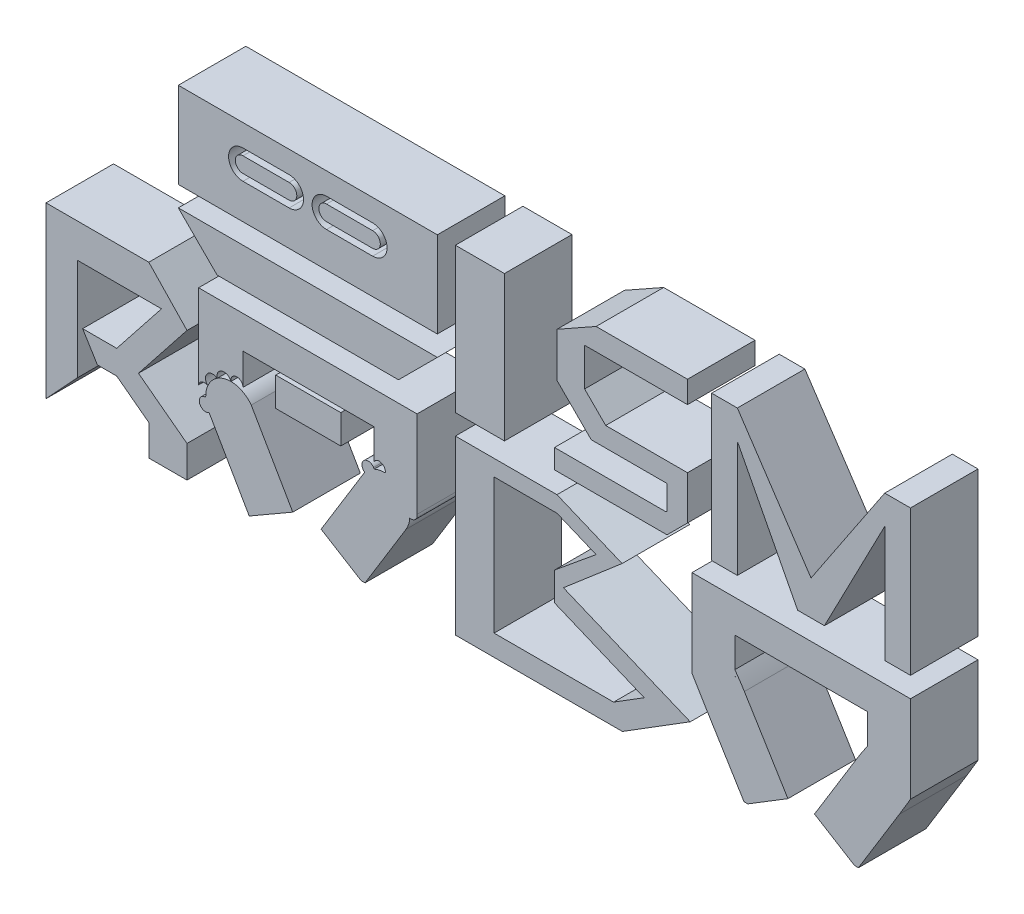
SolidWorks part; units mm, degrees
ref_plane "Front Plane" through (0, 0, 0) normal (0, 0, 1) x (1, 0, 0)
ref_plane "Top Plane" through (0, 0, 0) normal (0, 1, 0) x (1, 0, 0)
ref_plane "Right Plane" through (0, 0, 0) normal (1, 0, 0) x (0, 0, -1)
sketch "Sketch1" plane through (0, 0, 0) normal (0, 0, 1) x (1, 0, 0)
  line L0 (-96.2601, 0.8841) -> (-96.2601, 8.7422)
  line L1 (-108.1725, -11.9352) -> (-108.1725, 51.8543)
  line L2 (-108.1725, 51.8543) -> (-69.5108, 51.8543)
  line L3 (-69.5108, 51.8543) -> (-55.143, 36.8142)
  line L4 (-55.143, 36.8142) -> (-73.3959, 13.7377)
  line L5 (-73.3959, 13.7377) -> (-55.143, 0)
  line L6 (-55.143, 0) -> (-55.143, -11.9352)
  line L7 (-55.143, -11.9352) -> (-69.3611, -11.9352)
  line L8 (-69.3611, -11.9352) -> (-69.3611, -0.4586)
  line L9 (-69.3611, -0.4586) -> (-81.5859, 8.7422)
  line L10 (-81.5651, 17.7726) -> (-94.3869, 17.7726)
  line L11 (-94.3869, 17.7726) -> (-88.8416, 8.7422)
  line L12 (-88.8416, 8.7422) -> (-81.5859, 8.7422)
  line L13 (-81.5651, 17.7726) -> (-64.7268, 39.0605)
  line L14 (-64.7268, 39.0605) -> (-96.2601, 39.0605)
  line L15 (-96.2601, 39.0605) -> (-96.2601, 8.7422)
  line L16 (-96.2601, 0.8841) -> (-108.1725, -11.9352)
  line L17 (-31.7448, -11.9352) -> (-46.8387, 14.2083)
  line L18 (-31.7448, -11.9352) -> (-15.3667, -2.4793)
  line L19 (-15.3667, -2.4793) -> (-30.9907, 24.5823)
  line L26 (-21.7703, 38.9587) -> (2.6912, 38.9587)
  line L27 (-50.7939, 26.8876) -> (-50.7939, 52.8863)
  line L28 (11.4107, -12.579) -> (27.2355, 13.2281)
  line L29 (11.4107, -12.579) -> (-4.7114, -2.693)
  line L30 (-4.7114, -2.693) -> (11.6675, 24.0178)
  line L31 (-21.7703, 38.9587) -> (-21.7703, 28.0881)
  line L32 (-21.7703, 28.0881) -> (2.6912, 28.0881)
  line L33 (2.6912, 38.9587) -> (2.6912, 28.0881)
  line L34 (-9.5395, 28.0881) -> (-9.5395, 38.9587) construction
  line L35 (-21.7703, 33.5234) -> (2.6912, 33.5234) construction
  line L38 (-50.7939, 52.8863) -> (31.3755, 52.8863)
  line L39 (31.3755, 52.8863) -> (31.3755, 20.1587)
  line L40 (-50.7939, 21.2461) -> (-50.7939, 26.8876)
  line L41 (-34.0842, 28.7964) -> (-34.0842, 40.6137)
  line L42 (-34.0842, 40.6137) -> (15.2468, 40.6137)
  line L43 (15.2468, 40.6137) -> (15.2468, 29.3438)
  line L44 (45.7888, -11.9352) -> (45.7888, 52.8863)
  line L45 (45.7888, 52.8863) -> (83.9942, 52.8863)
  line L46 (83.9942, 52.8863) -> (98.7055, 46.7712)
  line L47 (98.7055, 46.7712) -> (108.4841, 42.7065)
  line L48 (108.4841, 42.7065) -> (86.4095, 23.7895)
  line L49 (86.4095, 23.7895) -> (134.1015, 3.9653)
  line L50 (134.1015, 3.9653) -> (108.6016, -11.9352)
  line L51 (108.6016, -11.9352) -> (45.7888, -11.9352)
  line L52 (60.3392, -4.0216) -> (105.2926, -4.0216)
  line L53 (105.2926, -4.0216) -> (116.8133, 3.1622)
  line L54 (116.8133, 3.1622) -> (82.8159, 17.2939)
  line L55 (82.8159, 17.2939) -> (73.8939, 17.2939)
  line L56 (73.8939, 17.2939) -> (64.2328, 27.6689)
  line L57 (64.2328, 27.6689) -> (82.8159, 27.6689)
  line L58 (82.8159, 27.6689) -> (98.7055, 40.7326)
  line L59 (98.7055, 40.7326) -> (83.9942, 46.8477)
  line L60 (83.9942, 46.8477) -> (60.3392, 46.8477)
  line L61 (60.3392, 46.8477) -> (60.3392, -4.0216)
  line L62 (83.0667, -11.9352) -> (83.0667, 52.8863)
  line L63 (138.8979, 13.2281) -> (134.7579, 20.1587)
  line L64 (155.5742, 22.2104) -> (154.4659, 24.0178)
  line L65 (150.8865, 40.6137) -> (150.8865, 29.3438)
  line L66 (200.7986, 40.6137) -> (150.8865, 40.6137)
  line L67 (175.8426, 52.8863) -> (175.8426, 40.6137)
  line L68 (196.9625, -12.579) -> (180.8403, -2.693)
  line L69 (134.7579, 52.8863) -> (134.7579, 20.1587)
  line L70 (216.9272, 52.8863) -> (134.7579, 52.8863)
  line L71 (196.9625, -12.579) -> (212.7872, 13.2281)
  line L72 (212.7872, 13.2281) -> (216.9272, 20.1587)
  line L76 (170.8448, -2.693) -> (155.5742, 22.2104)
  line L77 (154.7226, -12.579) -> (170.8448, -2.693)
  line L78 (154.7226, -12.579) -> (138.8979, 13.2281)
  line L79 (196.1109, 22.2104) -> (197.2192, 24.0178)
  line L81 (180.8403, -2.693) -> (196.1109, 22.2104)
  line L85 (200.7986, 40.6137) -> (200.7986, 29.3438)
  line L86 (216.9272, 52.8863) -> (216.9272, 20.1587)
  line L87 (-43.8191, 60.5063) -> (-58.4139, 75.1011)
  line L88 (-58.4139, 75.1011) -> (38.9955, 75.1011)
  line L89 (-43.8191, 60.5063) -> (24.4007, 60.5063)
  line L90 (38.9955, 75.1011) -> (24.4007, 60.5063)
  line L91 (-58.4139, 26.8876) -> (-58.4139, 60.5063) construction
  line L92 (-58.4139, 21.2461) -> (-58.4139, 26.8876) construction
  line L93 (38.9955, 60.5063) -> (38.9955, 20.1587) construction
  line L94 (-58.4139, 60.5063) -> (38.9955, 60.5063) construction
  line L95 (-69.3611, -11.9352) -> (-55.143, -11.9352)
  line L96 (10.3607, -11.9352) -> (11.8055, -11.9352)
  line L97 (45.7888, -11.9352) -> (108.6016, -11.9352)
  line L98 (154.3278, -11.9352) -> (155.7726, -11.9352)
  line L99 (195.9125, -11.9352) -> (197.3573, -11.9352)
  line L100 (-58.4139, 82.7211) -> (38.9955, 82.7211)
  line L102 (-46.9754, 52.8863) -> (27.557, 52.8863)
  line L104 (-46.9754, 52.8863) -> (-76.8102, 82.7211) construction
  line L105 (57.3918, 82.7211) -> (27.557, 52.8863) construction
  line L106 (-58.4139, 82.7211) -> (-58.4139, 115.0345)
  line L107 (-58.4139, 115.0345) -> (38.9955, 115.0345)
  line L108 (38.9955, 115.0345) -> (38.9955, 82.7211)
  line L109 (-76.8102, 82.7211) -> (57.3918, 82.7211) construction
  line L110 (-34.0842, 101.333) -> (-16.7424, 101.333) construction
  line L111 (-34.0842, 106.7565) -> (-16.7424, 106.7565)
  line L112 (-34.0842, 95.9095) -> (-16.7424, 95.9095)
  line L113 (-9.7092, 115.0345) -> (-9.7092, 82.7211)
  line L114 (14.6658, 101.333) -> (-2.676, 101.333) construction
  line L115 (14.6658, 106.7565) -> (-2.676, 106.7565)
  line L116 (14.6658, 95.9095) -> (-2.676, 95.9095)
  line L117 (-34.0842, 104.2165) -> (-16.7424, 104.2165)
  line L118 (-34.0842, 98.4495) -> (-16.7424, 98.4495)
  line L119 (14.6658, 104.2165) -> (-2.676, 104.2165)
  line L120 (14.6658, 98.4495) -> (-2.676, 98.4495)
  line L121 (45.7888, 60.5063) -> (45.7888, 115.0345)
  line L122 (45.7888, 115.0345) -> (64.2328, 115.0345)
  line L123 (64.2328, 115.0345) -> (64.2328, 60.5063)
  line L124 (64.2328, 60.5063) -> (45.7888, 60.5063)
  line L125 (83.0667, 60.5063) -> (125.3714, 60.5063)
  line L126 (125.3714, 60.5063) -> (133.0761, 68.211)
  line L127 (133.0761, 68.211) -> (133.0761, 84.584)
  line L128 (133.0761, 84.584) -> (102.3176, 84.584)
  line L129 (102.3176, 84.584) -> (94.387, 92.5145)
  line L130 (94.387, 92.5145) -> (94.387, 106.7565)
  line L131 (94.387, 106.7565) -> (133.0761, 106.7565)
  line L132 (133.0761, 106.7565) -> (133.0761, 115.0345)
  line L133 (133.0761, 115.0345) -> (98.7055, 115.0345)
  line L134 (98.7055, 115.0345) -> (83.9942, 106.7565)
  line L135 (83.9942, 106.7565) -> (83.9942, 90.0976)
  line L136 (83.9942, 90.0976) -> (96.8634, 77.2283)
  line L137 (96.8634, 77.2283) -> (125.3714, 77.2283)
  line L138 (125.3714, 77.2283) -> (125.3714, 68.211)
  line L139 (125.3714, 68.211) -> (124.9612, 67.8008)
  line L140 (124.9612, 67.8008) -> (83.0667, 67.8008)
  line L141 (83.0667, 67.8008) -> (83.0667, 60.5063)
  line L142 (142.1546, 60.5063) -> (142.1546, 115.0345)
  line L143 (142.1546, 115.0345) -> (151.8232, 115.0345)
  line L144 (216.9272, 115.0345) -> (216.9272, 60.5063)
  line L145 (216.9272, 60.5063) -> (207.2587, 60.5063)
  line L147 (207.2587, 60.5063) -> (207.2587, 104.2165)
  line L148 (207.2587, 104.2165) -> (184.5737, 60.5063)
  line L149 (184.5737, 60.5063) -> (179.5409, 60.5063)
  line L151 (151.8232, 60.5063) -> (151.8232, 104.2165)
  line L152 (151.8232, 104.2165) -> (174.5082, 60.5063)
  line L153 (142.1546, 60.5063) -> (151.8232, 60.5063)
  line L154 (179.5409, 73.5181) -> (207.2587, 115.0345)
  line L155 (179.5409, 73.5181) -> (151.8232, 115.0345)
  line L156 (207.2587, 115.0345) -> (216.9272, 115.0345)
  line L157 (179.5409, 60.5063) -> (174.5082, 60.5063)
  line L158 (-34.0842, 28.7964) -> (-34.0842, 27.2799)
  arc A0 (-29.9306, 22.7462) -> (-46.8387, 14.2083) centre (-38.6239, 18.9511) ccw
  arc A1 (-34.2557, 27.9281) -> (-34.4943, 27.4906) centre (-32.2952, 26.5752) ccw
  arc A2 (-34.4943, 27.4906) -> (-34.2557, 27.9281) centre (-36.3683, 28.7964) ccw
  arc A3 (-38.6239, 28.4368) -> (-43.8191, 26.8876) centre (-41.1863, 27.544) ccw
  arc A4 (-46.8387, 14.2083) -> (-48.1024, 18.5829) centre (-48.1433, 16.2013) cw
  arc A5 (-48.1024, 18.5829) -> (-48.5988, 18.5393) centre (-48.5493, 20.8228) cw
  arc A6 (-47.3173, 22.7462) -> (-43.8191, 26.8876) centre (-45.474, 24.7373) cw
  arc A7 (10.5592, 22.2104) -> (27.2355, 13.2281) centre (19.1491, 18.1866) cw
  arc A8 (11.6675, 24.0178) -> (15.2468, 26.8324) centre (13.0243, 25.9755) cw
  arc A9 (15.2468, 26.8324) -> (19.4001, 27.6689) centre (17.1548, 28.0881) cw
  arc A10 (19.4001, 27.6689) -> (24.5524, 25.9828) centre (21.9379, 26.7086) cw
  arc A11 (27.9398, 21.7503) -> (24.5524, 25.9828) centre (26.1498, 23.7895) ccw
  arc A12 (28.6145, 17.5677) -> (27.9398, 21.7503) centre (29.1205, 19.795) ccw
  arc A13 (27.2355, 13.2281) -> (28.6145, 17.5677) centre (28.5923, 15.1858) ccw
  arc A14 (-19.1705, 28.0881) -> (-14.1284, 28.0881) centre (-16.6494, 28.0881) ccw
  arc A15 (0.0914, 28.0881) -> (-4.9507, 28.0881) centre (-2.4297, 28.0881) cw
  arc A16 (138.7851, 13.4169) -> (138.8979, 13.2281) centre (146.9843, 18.1866) ccw
  arc A17 (154.4659, 24.0178) -> (150.8865, 29.3438) centre (88.7772, -16.2621) ccw
  arc A18 (137.0238, 17.5109) -> (137.5189, 17.5677) centre (137.541, 15.1858) cw
  arc A19 (137.5189, 17.5677) -> (137.0238, 17.5109) centre (137.0128, 19.795) cw
  arc A22 (150.8865, 26.8324) -> (151.1135, 27.2761) centre (148.9786, 28.0881) ccw
  arc A23 (151.1135, 27.2761) -> (150.8865, 26.8324) centre (153.109, 25.9755) ccw
  arc A24 (197.2192, 24.0178) -> (200.7986, 29.3438) centre (262.9079, -16.2621) cw
  arc A25 (-34.0842, 106.7565) -> (-34.0842, 95.9095) centre (-34.0842, 101.333) ccw
  arc A26 (-16.7424, 95.9095) -> (-16.7424, 106.7565) centre (-16.7424, 101.333) ccw
  arc A27 (14.6658, 106.7565) -> (14.6658, 95.9095) centre (14.6658, 101.333) cw
  arc A28 (-2.676, 95.9095) -> (-2.676, 106.7565) centre (-2.676, 101.333) cw
  arc A29 (-16.7424, 98.4495) -> (-16.7424, 104.2165) centre (-16.7424, 101.333) ccw
  arc A30 (-34.0842, 104.2165) -> (-34.0842, 98.4495) centre (-34.0842, 101.333) ccw
  arc A31 (-2.676, 98.4495) -> (-2.676, 104.2165) centre (-2.676, 101.333) cw
  arc A32 (14.6658, 104.2165) -> (14.6658, 98.4495) centre (14.6658, 101.333) cw
  arc A33 (-34.0842, 28.7964) -> (-38.6239, 28.4368) centre (-36.3683, 28.7964) ccw
  arc A34 (-50.7939, 21.2461) -> (-47.3173, 22.7462) centre (-48.5493, 20.8228) cw
  arc A35 (-50.7939, 20.4238) -> (-48.5778, 18.5433) centre (-48.5493, 20.8228) ccw
  arc A36 (-50.7939, 20.4238) -> (-50.7869, 21.2592) centre (-48.5493, 20.8228) cw
  point P119 (175.8426, 40.6137)
  point P150 (-25.4133, 101.333)
  point P159 (5.9949, 101.333)
  dimension "D1" = 7.62
  dimension "D2" = 7.62
  dimension "D3" = 2.54
  dimension "D4" = 2.54
extrude "Boss-Extrude2" add sketch "Sketch1" along normal blind 25.4 contours L51 L62 L52 L61 L60 L45 L44 | L62 L51 L50 L49 L48 L47 L46 L45 L60 L59 L58 L54 L53 L52 | L16 L0 L15 L14 L13 L10 L11 L12 L9 L8 L7 L6 L5 L4 L3 L2 L1 | A12 L39 L38 L27 L40 A5 A6 A3 A2 L41 L42 L43 A9 A10 A11 | L19 A0 L17 L18 | L33 L26 L31 L32 | A7 A9 A8 | A7 L30 L29 L96 L28 | A10 A7 | A7 A11 | A13 A12 A7 | A0 A5 A4 | L90 L88 L87 L89 | L107 L113 L100 L108 L116 A28 L115 A27 | L113 L107 L106 L100 A26 L112 A25 L111 | L117 A30 L118 A29 | A32 L119 A31 L120 | L124 L123 L122 L121 | L140 L141 L125 L126 L127 L128 L129 L130 L131 L132 L133 L134 L135 L136 L137 L138 L139 | L157 L149 L148 L147 L145 L144 L156 L154 L155 L143 L142 L153 L151 L152 | A24 L79 L81 L68 L99 L71 L72 L86 L70 L67 L66 L85 | L64 A17 L65 L66 L67 L70 L69 L63 L78 L98 L77 L76 A23 A22 A18 A19
